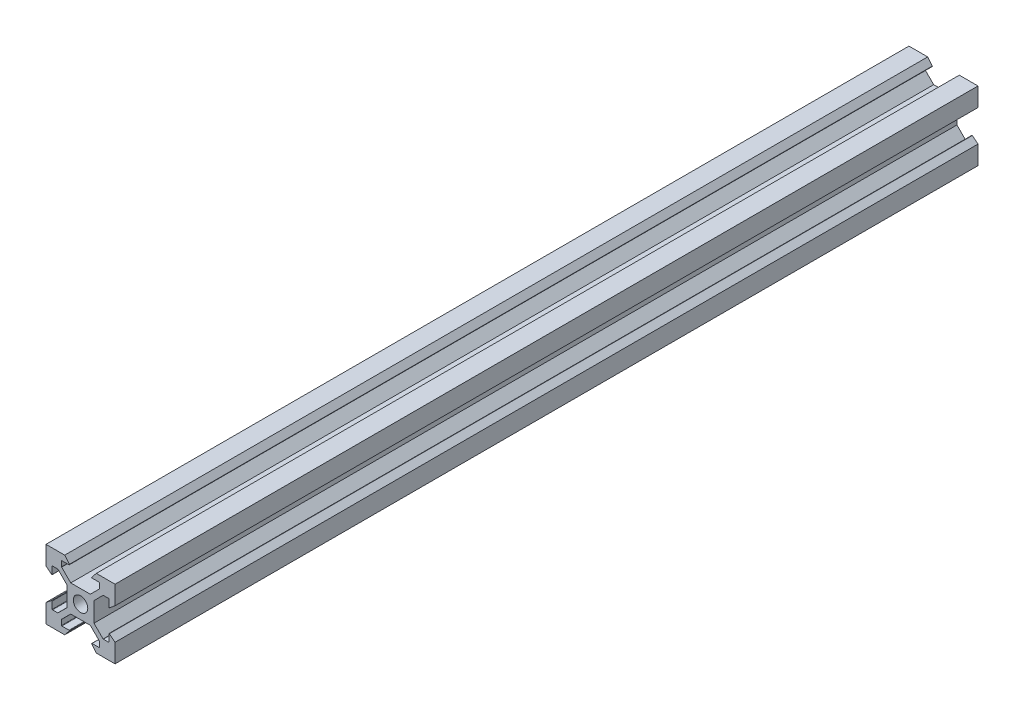
SolidWorks part; units mm, degrees
ref_plane "Front Plane" through (0, 0, 0) normal (0, 0, 1) x (1, 0, 0)
ref_plane "Top Plane" through (0, 0, 0) normal (0, 1, 0) x (1, 0, 0)
ref_plane "Right Plane" through (0, 0, 0) normal (1, 0, 0) x (0, 0, -1)
sketch "Sketch1" plane through (0, 0, 0) normal (0, 0, 1) x (1, 0, 0)
  line L0 (-2.8393, 3.9) -> (-5.4707, 6.5314)
  line L1 (-10, 10) -> (-4.58, 10)
  line L2 (-10, 10) -> (-10, 4.58)
  line L3 (-10, -10) -> (-4.58, -10)
  line L4 (10, 10) -> (10, 4.58)
  line L5 (-10, 10) -> (-3.9, 3.9) construction
  line L6 (-10, -10) -> (-4.061, -4.061) construction
  line L7 (-2.8393, 3.9) -> (2.8393, 3.9)
  line L8 (-3.9, 2.8393) -> (-3.9, -2.8393)
  line L9 (-2.8393, -3.9) -> (2.8393, -3.9)
  line L10 (3.9, 2.8393) -> (3.9, -2.8393)
  line L11 (-1.4849, 1.4849) -> (3.9, -3.9) construction
  line L12 (-3.9, -3.9) -> (1.4849, 1.4849) construction
  line L13 (-5.5, 6.6021) -> (-5.5, 8.1)
  line L14 (-5.4, 8.2) -> (-3.3344, 8.2)
  line L15 (-3.2566, 8.3629) -> (-4.58, 10)
  line L16 (0, 0) -> (0, 5.2663) construction
  line L17 (-3.9, 2.8393) -> (-6.5314, 5.4707)
  line L18 (-6.6021, 5.5) -> (-8.1, 5.5)
  line L19 (-8.2, 5.4) -> (-8.2, 3.3344)
  line L20 (-8.3629, 3.2566) -> (-10, 4.58)
  line L21 (8.3629, 3.2566) -> (10, 4.58)
  line L22 (8.2, 5.4) -> (8.2, 3.3344)
  line L23 (6.6021, 5.5) -> (8.1, 5.5)
  line L24 (3.9, 2.8393) -> (6.5314, 5.4707)
  line L25 (3.2566, 8.3629) -> (4.58, 10)
  line L26 (5.4, 8.2) -> (3.3344, 8.2)
  line L27 (2.8393, 3.9) -> (5.4707, 6.5314)
  line L28 (5.5, 6.6021) -> (5.5, 8.1)
  line L29 (55, 0) -> (-55, 0) construction
  line L30 (-8.3629, -3.2566) -> (-10, -4.58)
  line L31 (-8.2, -5.4) -> (-8.2, -3.3344)
  line L32 (-6.6021, -5.5) -> (-8.1, -5.5)
  line L33 (-3.9, -2.8393) -> (-6.5314, -5.4707)
  line L34 (-2.8393, -3.9) -> (-5.4707, -6.5314)
  line L35 (-5.5, -6.6021) -> (-5.5, -8.1)
  line L36 (-5.4, -8.2) -> (-3.3344, -8.2)
  line L37 (-3.2566, -8.3629) -> (-4.58, -10)
  line L38 (8.3629, -3.2566) -> (10, -4.58)
  line L39 (8.2, -5.4) -> (8.2, -3.3344)
  line L40 (6.6021, -5.5) -> (8.1, -5.5)
  line L41 (3.9, -2.8393) -> (6.5314, -5.4707)
  line L42 (2.8393, -3.9) -> (5.4707, -6.5314)
  line L43 (5.5, -6.6021) -> (5.5, -8.1)
  line L44 (5.4, -8.2) -> (3.3344, -8.2)
  line L45 (3.2566, -8.3629) -> (4.58, -10)
  line L46 (3.9, 3.9) -> (10, 10) construction
  line L47 (3.2459, -3.2459) -> (10, -10) construction
  line L48 (-10, -4.58) -> (-10, -10)
  line L49 (4.58, -10) -> (10, -10)
  line L50 (10, -4.58) -> (10, -10)
  line L51 (4.58, 10) -> (10, 10)
  circle A0 centre (0, 0) radius 2.1
  arc A1 (-5.4707, 6.5314) -> (-5.5, 6.6021) centre (-5.4, 6.6021) cw
  arc A2 (-5.5, 8.1) -> (-5.4, 8.2) centre (-5.4, 8.1) cw
  arc A3 (-3.3344, 8.2) -> (-3.2566, 8.3629) centre (-3.3344, 8.3) ccw
  arc A4 (-6.5314, 5.4707) -> (-6.6021, 5.5) centre (-6.6021, 5.4) ccw
  arc A5 (-8.1, 5.5) -> (-8.2, 5.4) centre (-8.1, 5.4) ccw
  arc A6 (-8.2, 3.3344) -> (-8.3629, 3.2566) centre (-8.3, 3.3344) cw
  arc A7 (8.2, 3.3344) -> (8.3629, 3.2566) centre (8.3, 3.3344) ccw
  arc A8 (8.1, 5.5) -> (8.2, 5.4) centre (8.1, 5.4) cw
  arc A9 (6.5314, 5.4707) -> (6.6021, 5.5) centre (6.6021, 5.4) cw
  arc A10 (3.3344, 8.2) -> (3.2566, 8.3629) centre (3.3344, 8.3) cw
  arc A11 (5.5, 8.1) -> (5.4, 8.2) centre (5.4, 8.1) ccw
  arc A12 (5.4707, 6.5314) -> (5.5, 6.6021) centre (5.4, 6.6021) ccw
  arc A13 (-8.2, -3.3344) -> (-8.3629, -3.2566) centre (-8.3, -3.3344) ccw
  arc A14 (-8.1, -5.5) -> (-8.2, -5.4) centre (-8.1, -5.4) cw
  arc A15 (-6.5314, -5.4707) -> (-6.6021, -5.5) centre (-6.6021, -5.4) cw
  arc A16 (-5.4707, -6.5314) -> (-5.5, -6.6021) centre (-5.4, -6.6021) ccw
  arc A17 (-5.5, -8.1) -> (-5.4, -8.2) centre (-5.4, -8.1) ccw
  arc A18 (-3.3344, -8.2) -> (-3.2566, -8.3629) centre (-3.3344, -8.3) cw
  arc A19 (8.2, -3.3344) -> (8.3629, -3.2566) centre (8.3, -3.3344) cw
  arc A20 (8.1, -5.5) -> (8.2, -5.4) centre (8.1, -5.4) ccw
  arc A21 (6.5314, -5.4707) -> (6.6021, -5.5) centre (6.6021, -5.4) ccw
  arc A22 (5.4707, -6.5314) -> (5.5, -6.6021) centre (5.4, -6.6021) cw
  arc A23 (5.5, -8.1) -> (5.4, -8.2) centre (5.4, -8.1) cw
  arc A24 (3.3344, -8.2) -> (3.2566, -8.3629) centre (3.3344, -8.3) ccw
  point P0 (0, 0)
  point P6 (0, 0)
  point P25 (-3.125, 8.2)
  dimension "D5" = 4.2
  dimension "D11" = 0.1
  dimension "D1" = 20
  dimension "D3" = 7.8
  dimension "D4" = 7.8
  dimension "D6" = 0.75
  dimension "D7" = 4.3
  dimension "D8" = 4.58
  dimension "D9" = 3.125
  dimension "D10" = 5.5
extrude "Boss-Extrude1" add sketch "Sketch1" along normal blind 250
